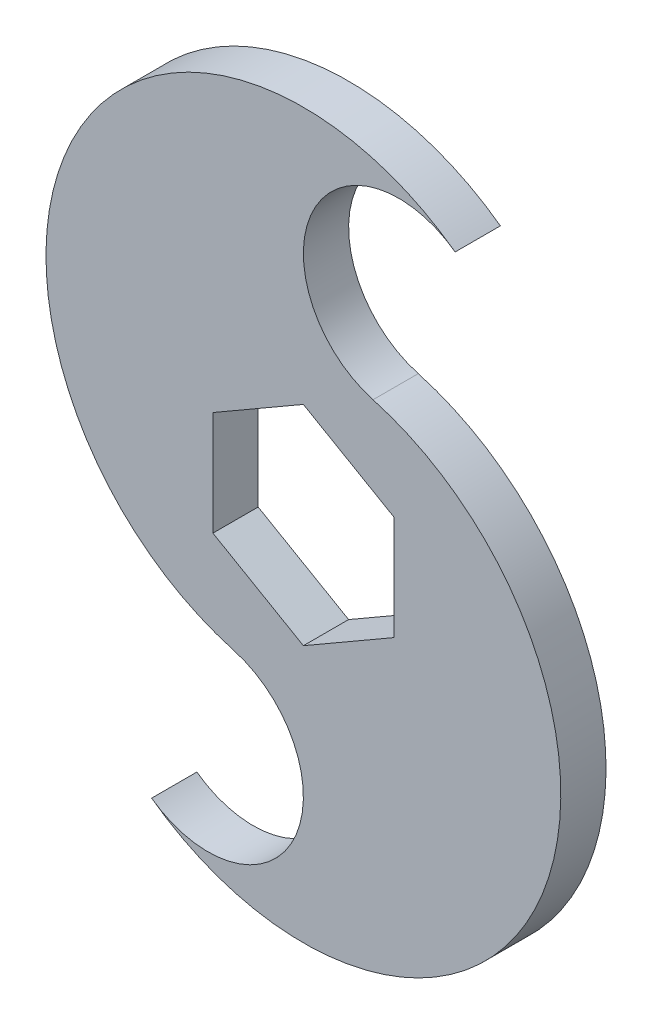
SolidWorks part; units mm, degrees
ref_plane "Front Plane" through (0, 0, 0) normal (0, 0, 1) x (1, 0, 0)
ref_plane "Top Plane" through (0, 0, 0) normal (0, 1, 0) x (1, 0, 0)
ref_plane "Right Plane" through (0, 0, 0) normal (1, 0, 0) x (0, 0, -1)
sketch "Sketch1" plane through (0, 0, 0) normal (0, 0, 1) x (1, 0, 0)
  line L0 (0, 50.8) -> (0, 14.6647) construction
  line L5 (0, 14.6647) -> (-12.7, 7.3323)
  line L6 (-12.7, 7.3323) -> (-12.7, -7.3323)
  line L7 (-12.7, -7.3323) -> (0, -14.6647)
  line L8 (0, -14.6647) -> (12.7, -7.3323)
  line L9 (12.7, -7.3323) -> (12.7, 7.3323)
  line L10 (12.7, 7.3323) -> (0, 14.6647)
  line L11 (0, -14.6647) -> (0, -50.8) construction
  circle A0 centre (0, 0) radius 12.7 construction
  arc A1 (-21.3049, -43.8514) -> (9.7766, 20.1229) centre (0, -14.6647) ccw
  circle A2 centre (0, 0) radius 50.8 construction
  arc A3 (21.3049, 43.8514) -> (-9.7766, -20.1229) centre (0, 14.6647) ccw
  arc A4 (21.3049, 43.8514) -> (9.7766, 20.1229) centre (13.4028, 33.0259) ccw
  arc A5 (-9.7766, -20.1229) -> (-21.3049, -43.8514) centre (-13.4028, -33.0259) cw
  point P11 (10.3208, 12.4543)
  dimension "D2" = 101.6
  dimension "D1" = 25.4
extrude "Boss-Extrude2" add sketch "Sketch1" along normal mid plane 6.35
